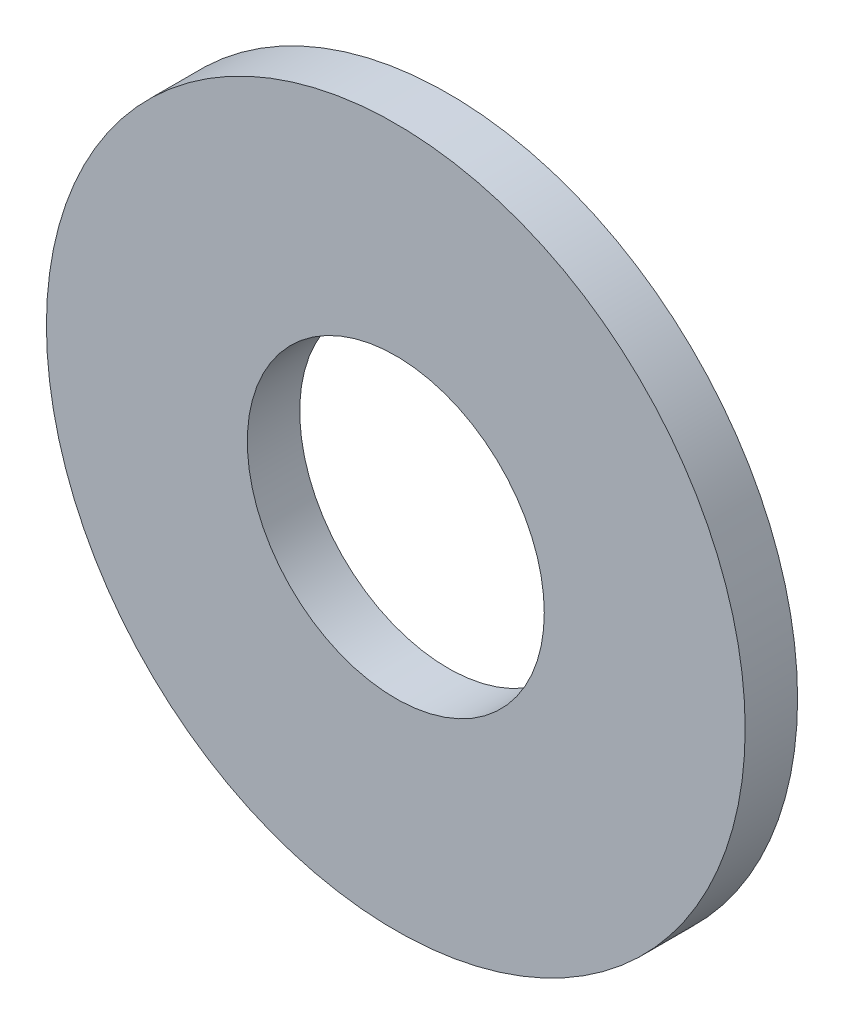
SolidWorks part; units mm, degrees
ref_plane "Front Plane" through (0, 0, 0) normal (0, 0, 1) x (1, 0, 0)
ref_plane "Top Plane" through (0, 0, 0) normal (0, 1, 0) x (1, 0, 0)
ref_plane "Right Plane" through (0, 0, 0) normal (1, 0, 0) x (0, 0, -1)
sketch "Sketch1" plane through (0, 0, 0) normal (0, 0, 1) x (1, 0, 0)
  circle A0 centre (0, 0) radius 2
  circle A1 centre (0, 0) radius 0.85
  dimension "OD" = 1.7
  dimension "ID" = 4
extrude "Boss-Extrude1" add sketch "Sketch1" along normal blind 0.3
